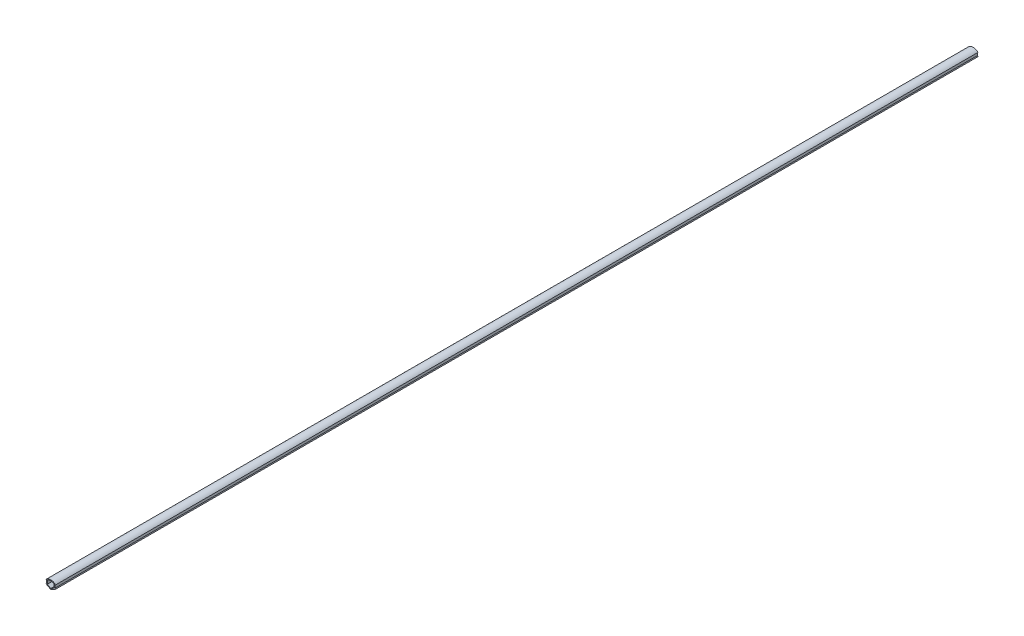
SolidWorks part; units mm, degrees
material "Пластик"
ref_plane "Спереди" through (0, 0, 0) normal (0, 0, 1) x (1, 0, 0)
ref_plane "Сверху" through (0, 0, 0) normal (0, 1, 0) x (1, 0, 0)
ref_plane "Справа" through (0, 0, 0) normal (1, 0, 0) x (0, 0, -1)
sketch "Эскиз1" plane through (0, 0, 0) normal (0, 0, 1) x (1, 0, 0)
  line L42 (0, 0) -> (-5.2, 3.0022)
  line L43 (-5.2, 3.0022) -> (-4.7, 3.8682)
  line L44 (-4.7, 3.8682) -> (-4.7, 7.0749)
  line L45 (-4.7, 7.0749) -> (-5.2048, 7.0749)
  line L46 (0, 0) -> (0, 9.3) construction
  line L47 (4.7, 7.0749) -> (5.2048, 7.0749)
  line L48 (4.7, 3.8682) -> (4.7, 7.0749)
  line L49 (5.2, 3.0022) -> (4.7, 3.8682)
  line L50 (0, 0) -> (5.2, 3.0022)
  line L51 (0, 1.1547) -> (-3.7, 3.2909)
  line L52 (-3.7, 3.2909) -> (-3.7, 7.0749)
  line L53 (3.7, 3.2909) -> (3.7, 7.0749)
  line L54 (0, 0) -> (5.2, 3.0022)
  line L55 (0, 1.1547) -> (3.7, 3.2909)
  arc A2 (-5.2048, 7.0749) -> (5.2048, 7.0749) centre (0, 2.1) cw
  arc A3 (-3.7, 7.0749) -> (3.7, 7.0749) centre (0, 2.1) cw
  dimension "D5" = 7.2
  dimension "D6" = 6.2
  dimension "D1" = 9.4
  dimension "D2" = 9.3
  dimension "D3" = 1
  dimension "D4" = 1
  dimension "D7" = 60
  dimension "D8" = 1
extrude "Бобышка-Вытянуть1" add sketch "Эскиз1" along normal blind 1000 contours L42 L46 L51 L52 A3 A2 L45 L44 L43 | L46 L50 L49 L48 L47 A2 A3 L53 L55
